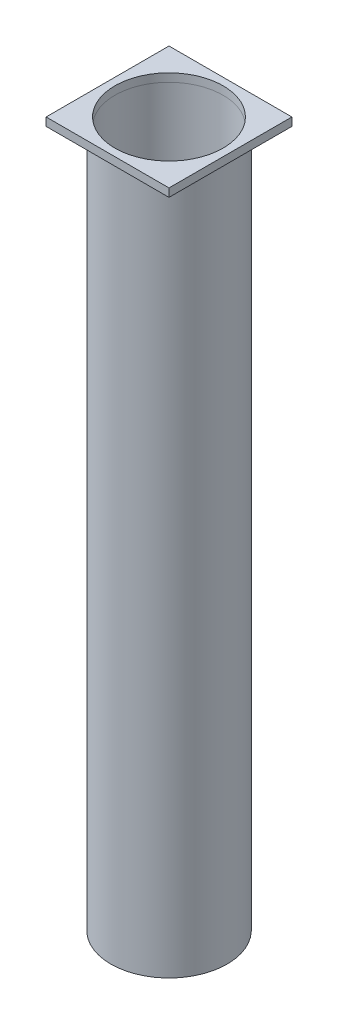
SolidWorks part; units mm, degrees
ref_plane "Front Plane" through (0, 0, 0) normal (0, 0, 1) x (1, 0, 0)
ref_plane "Top Plane" through (0, 0, 0) normal (0, 1, 0) x (1, 0, 0)
ref_plane "Right Plane" through (0, 0, 0) normal (1, 0, 0) x (0, 0, -1)
sketch "Sketch1" plane through (0, 0, 0) normal (0, 1, 0) x (1, 0, 0)
  circle A0 centre (0, 0) radius 66
  circle A1 centre (0, 0) radius 71
  dimension "D1" = 132
  dimension "D2" = 142
extrude "Boss-Extrude1" add sketch "Sketch1" along normal blind 850
sketch "Sketch2" plane through (0, 850, 0) normal (0, 1, 0) x (1, 0, 0)
  line L1 (-75, -75) -> (75, -75)
  line L2 (-75, -75) -> (-75, 75)
  line L3 (-75, 75) -> (75, 75)
  line L4 (75, -75) -> (75, 75)
  line L5 (-75, -75) -> (75, 75) construction
  line L6 (-75, 75) -> (75, -75) construction
  circle A1 centre (0, 0) radius 66
  dimension "D1" = 150
  dimension "D2" = 150
extrude "Boss-Extrude2" add sketch "Sketch2" along normal blind 10 separate body
